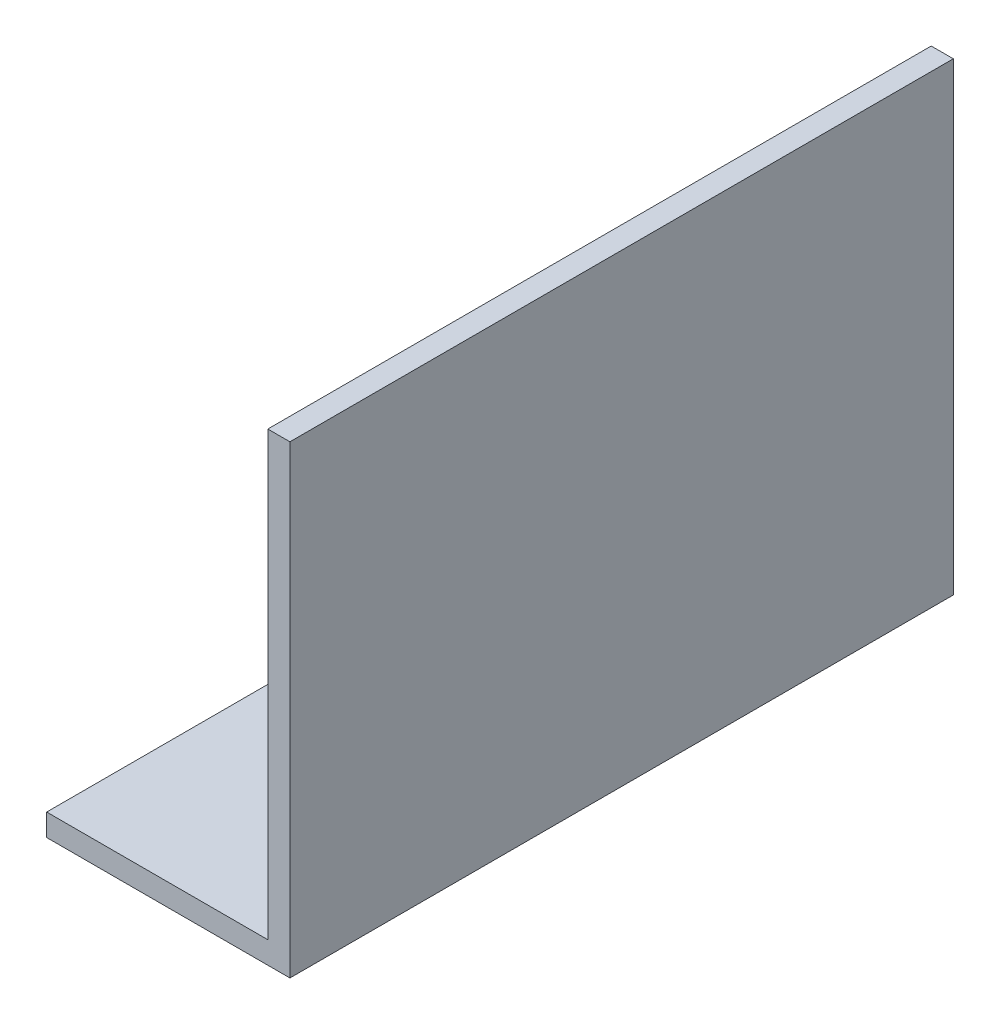
SolidWorks part; units mm, degrees
ref_plane "Plan de face" through (0, 0, 0) normal (0, 0, 1) x (1, 0, 0)
ref_plane "Plan de dessus" through (0, 0, 0) normal (0, 1, 0) x (1, 0, 0)
ref_plane "Plan de droite" through (0, 0, 0) normal (1, 0, 0) x (0, 0, -1)
sketch "Esquisse1" plane through (0, 0, 0) normal (0, 0, 1) x (1, 0, 0)
  line L0 (0, 0) -> (20, 0)
  line L1 (20, 0) -> (20, 40)
  dimension "D1" = 20
  dimension "D2" = 40
extrude "Extru.-Mince1" add sketch "Esquisse1" along normal blind 60 thin
